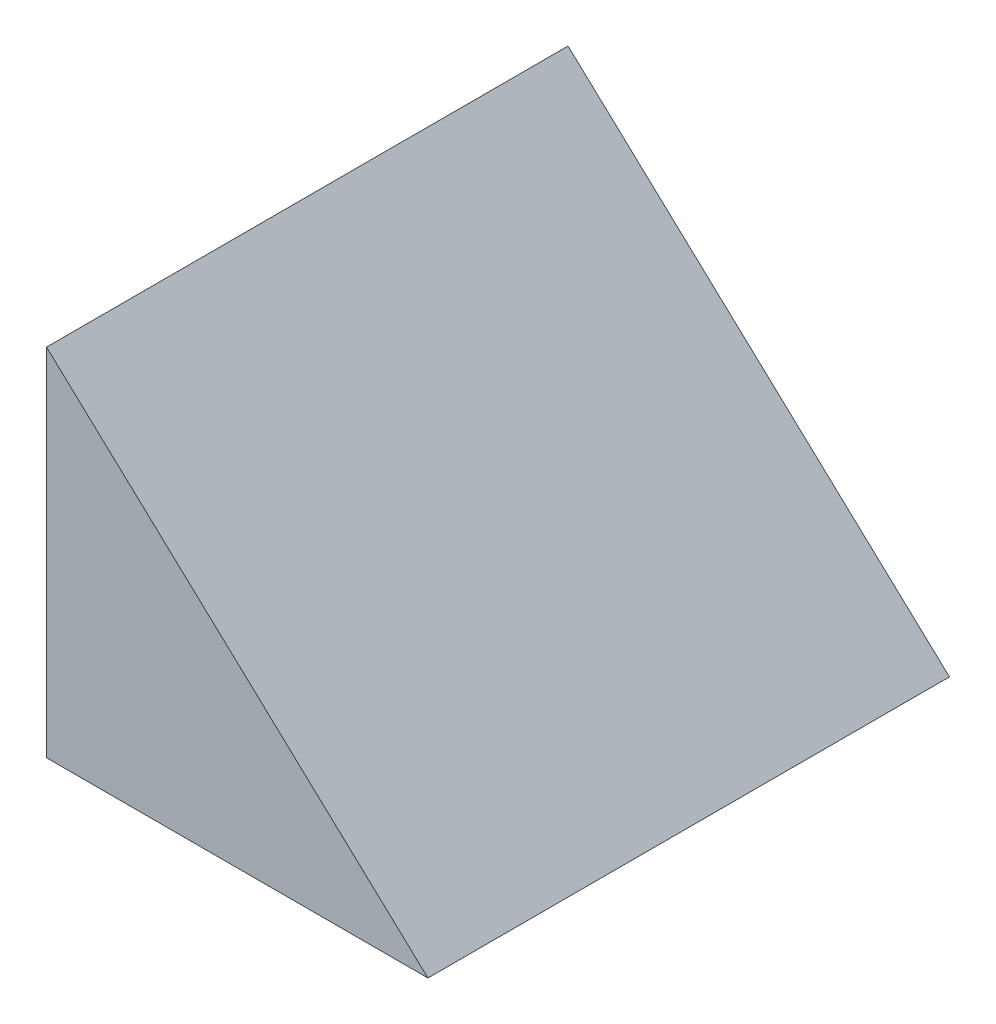
SolidWorks part; units mm, degrees
ref_plane "Front Plane" through (0, 0, 0) normal (0, 0, 1) x (1, 0, 0)
ref_plane "Top Plane" through (0, 0, 0) normal (0, 1, 0) x (1, 0, 0)
ref_plane "Right Plane" through (0, 0, 0) normal (1, 0, 0) x (0, 0, -1)
sketch "Sketch1" plane through (0, 0, 0) normal (0, 0, 1) x (1, 0, 0)
  line L0 (0, 0) -> (21.9406, 0)
  line L1 (21.9406, 0) -> (0, 20.46)
  line L2 (0, 20.46) -> (0, 0)
  dimension "D1" = 43
  dimension "D2" = 30
extrude "Boss-Extrude1" add sketch "Sketch1" against normal blind 30
sketch "Sketch3" plane through (0, 0, 0) normal (0, -1, 0) x (1, 0, 0)
  line L1 (0, -15) -> (21.9406, -15) construction
  line L3 (0, -30) -> (0, 0) construction
  line L4 (21.9406, -30) -> (21.9406, 0) construction
  circle A1 centre (11.9406, -15) radius 1.5
  dimension "D4" = 3
  dimension "D1" = 10
extrude "Cut-Extrude1" cut sketch "Sketch3" against normal blind 7.5
sketch "Sketch6" plane through (0, 0, 0) normal (-1, 0, 0) x (0, 0, 1)
  line L0 (-30, 0) -> (0, 0) construction
  line L1 (-28.5, 0) -> (-1.5, 0)
  line L2 (-28.5, 0) -> (-28.5, 13.5)
  line L3 (-28.5, 13.5) -> (-1.5, 13.5)
  line L4 (-1.5, 0) -> (-1.5, 13.5)
  line L5 (0, 20.46) -> (0, 0) construction
  line L6 (-30, 20.46) -> (-30, 0) construction
  dimension "D1" = 1.5
  dimension "D2" = 1.5
  dimension "D3" = 13.5
extrude "Cut-Extrude2" cut sketch "Sketch6" against normal blind 6
